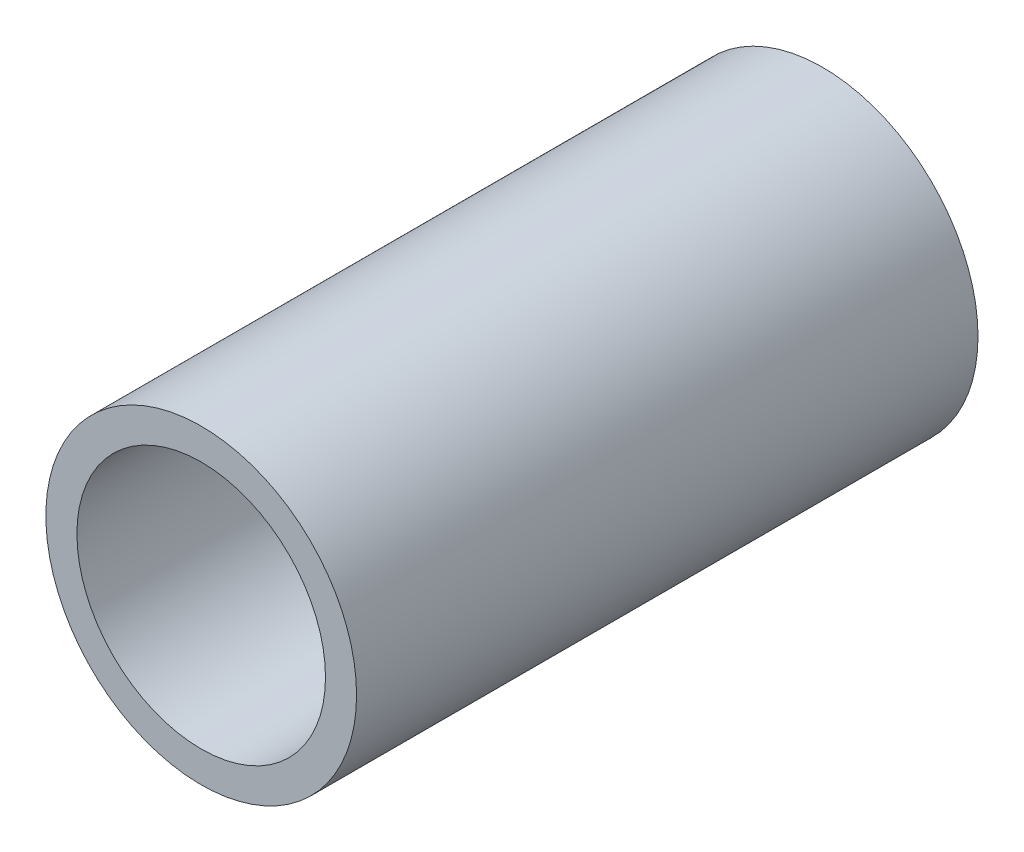
SolidWorks part; units mm, degrees
ref_plane "Front Plane" through (0, 0, 0) normal (0, 0, 1) x (1, 0, 0)
ref_plane "Top Plane" through (0, 0, 0) normal (0, 1, 0) x (1, 0, 0)
ref_plane "Right Plane" through (0, 0, 0) normal (1, 0, 0) x (0, 0, -1)
sketch "Sketch1" plane through (0, 0, 0) normal (0, 0, 1) x (1, 0, 0)
  circle A0 centre (0, 0) radius 1
  circle A1 centre (0, 0) radius 1.25
  dimension "D1" = 2
  dimension "D2" = 2.5
extrude "Boss-Extrude1" add sketch "Sketch1" along normal blind 5
